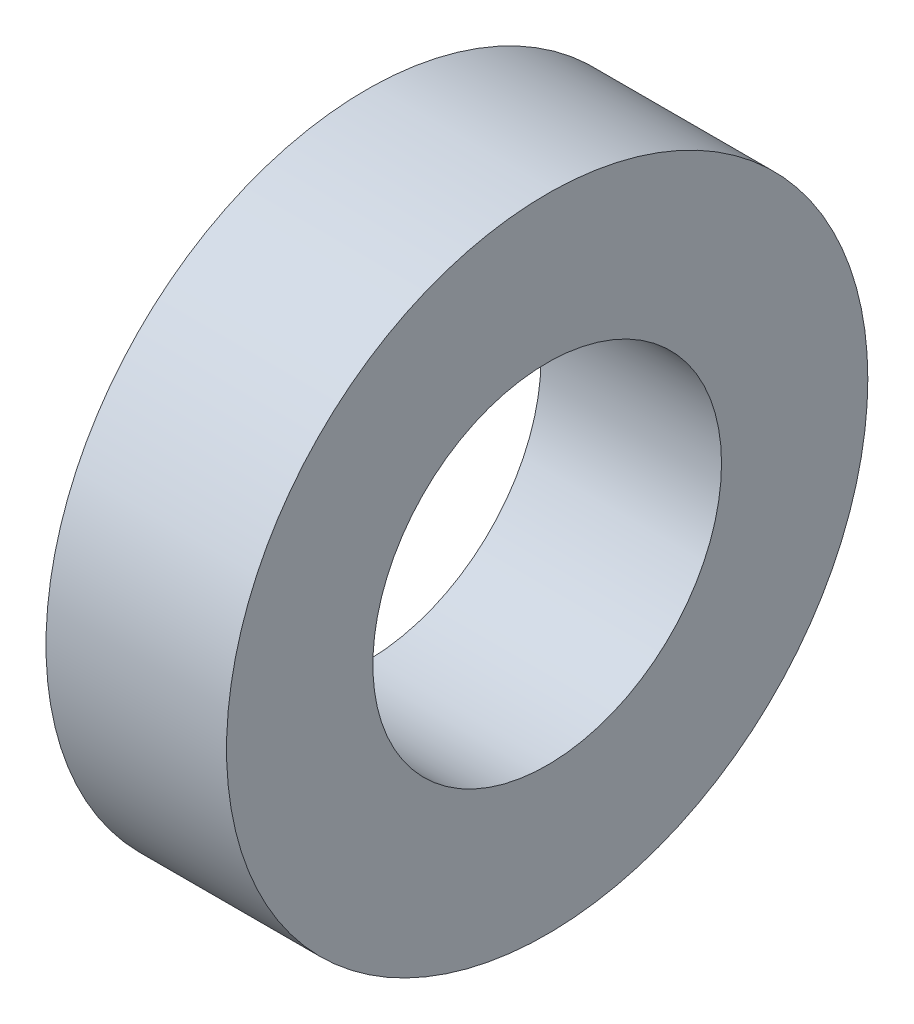
SolidWorks part; units mm, degrees
ref_plane "Front Plane" through (0, 0, 0) normal (0, 0, 1) x (1, 0, 0)
ref_plane "Top Plane" through (0, 0, 0) normal (0, 1, 0) x (1, 0, 0)
ref_plane "Right Plane" through (0, 0, 0) normal (1, 0, 0) x (0, 0, -1)
sketch "Sketch1" plane through (0, 0, 0) normal (1, 0, 0) x (0, 0, -1)
  circle A0 centre (0, 0) radius 2.6162
  circle A1 centre (0, 0) radius 1.4224
  dimension "OD" = 5.2324
  dimension "ID" = 2.8448
extrude "Boss-Extrude1" add sketch "Sketch1" along normal blind 1.4732
